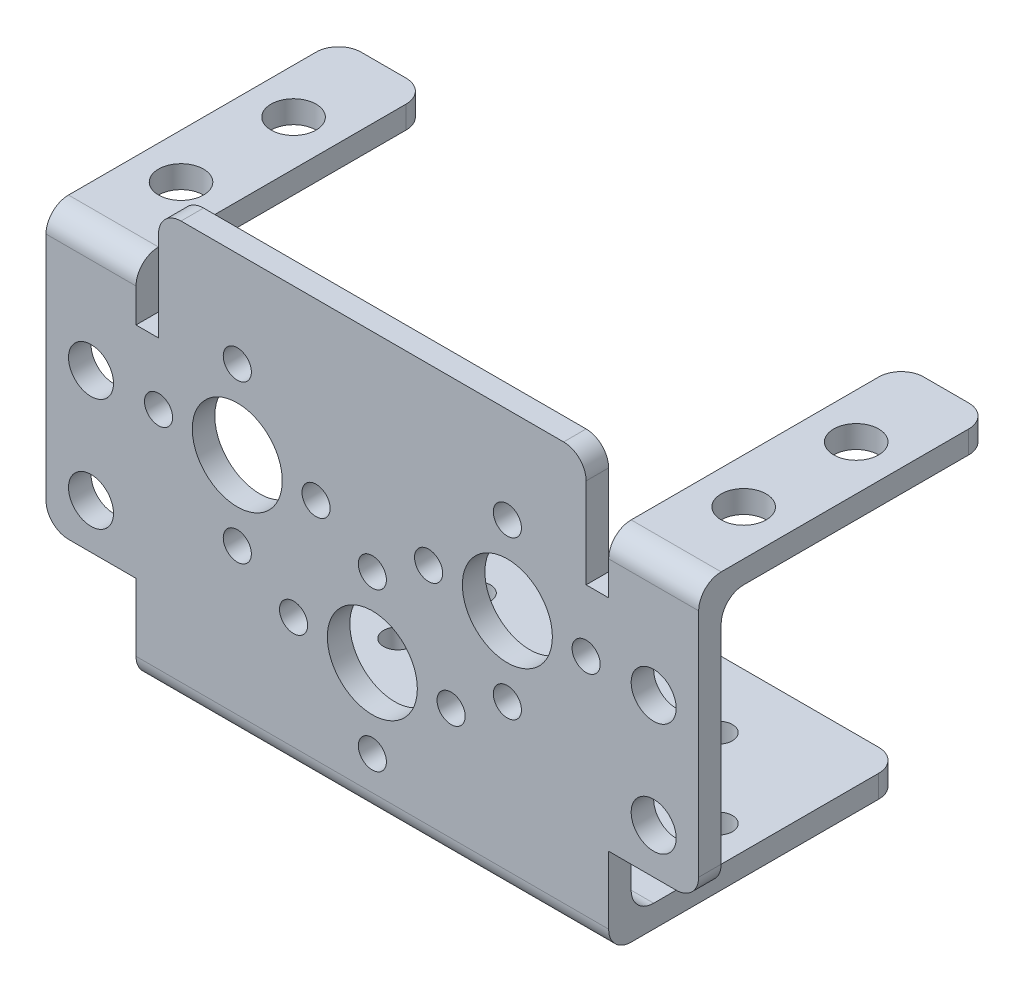
SolidWorks part; units mm, degrees
ref_plane "前视基准面" through (0, 0, 0) normal (0, 0, 1) x (1, 0, 0)
ref_plane "上视基准面" through (0, 0, 0) normal (0, 1, 0) x (1, 0, 0)
ref_plane "右视基准面" through (0, 0, 0) normal (1, 0, 0) x (0, 0, -1)
sketch "草图1" plane through (0, 0, 0) normal (0, 1, 0) x (1, 0, 0)
  line L0 (0, 0) -> (12, 0) construction
  line L1 (-21, 13) -> (21, 13)
  line L2 (-21, 13) -> (-21, -13)
  line L3 (-21, -13) -> (21, -13)
  line L4 (21, 13) -> (21, -13)
  line L5 (-21, 13) -> (21, -13) construction
  line L6 (-21, -13) -> (21, 13) construction
  line L7 (0, 0) -> (0, -13) construction
  circle A0 centre (10.75, 0) radius 1.25
  circle A1 centre (10.75, 0) radius 7 construction
  circle A2 centre (3.75, 0) radius 1.25
  circle A3 centre (10.75, 7) radius 1.25
  circle A4 centre (17.75, 0) radius 1.25
  circle A5 centre (10.75, -7) radius 1.25
  circle A6 centre (-10.75, -7) radius 1.25
  circle A7 centre (-17.75, 0) radius 1.25
  circle A8 centre (-10.75, 0) radius 1.25
  circle A9 centre (-10.75, 7) radius 1.25
  circle A10 centre (-3.75, 0) radius 1.25
  point P0 (0, 0)
  point P22 (10.75, 0)
  dimension "D4" = 2.5
  dimension "D5" = 14
  dimension "D6" = 2.5
  dimension "D8" = 7
  dimension "D1" = 42
  dimension "D2" = 26
  dimension "D3" = 12
  dimension "D9" = 7
  dimension "D7" = 4
extrude "凸台-拉伸1" add sketch "草图1" along normal blind 2
sketch "草图2" plane through (0, 0, 13) normal (0, 0, 1) x (1, 0, 0)
  line L3 (21, 0) -> (-21, 0)
  line L4 (0, 0) -> (0, 12) construction
  line L5 (0, 12) -> (0, 22) construction
  line L6 (0, 22) -> (12, 22) construction
  line L7 (0, 0) -> (0, 37.5) construction
  line L8 (0, 37.5) -> (-19, 37.5)
  line L9 (0, 37.5) -> (19, 37.5)
  line L10 (-19, 37.5) -> (-19, 27.5)
  line L11 (19, 37.5) -> (19, 27.5)
  line L12 (-19, 27.5) -> (-21, 27.5)
  line L13 (19, 27.5) -> (21, 27.5)
  line L16 (-21, 27.5) -> (-21, 32.5)
  line L17 (-21, 32.5) -> (-29, 32.5)
  line L18 (-29, 32.5) -> (-29, 8)
  line L19 (-29, 8) -> (-21, 8)
  line L20 (-21, 8) -> (-21, 0)
  line L21 (21, 8) -> (21, 0)
  line L22 (29, 8) -> (21, 8)
  line L23 (29, 32.5) -> (29, 8)
  line L24 (21, 32.5) -> (29, 32.5)
  line L25 (21, 27.5) -> (21, 32.5)
  line L26 (-19, 22) -> (-25, 22) construction
  line L27 (-25, 22) -> (-25, 12) construction
  circle A0 centre (0, 12) radius 4
  circle A1 centre (0, 12) radius 7 construction
  circle A2 centre (0, 19) radius 1.25
  circle A3 centre (7, 12) radius 1.25
  circle A4 centre (0, 5) radius 1.25
  circle A5 centre (-7, 12) radius 1.25
  circle A6 centre (12, 22) radius 4
  circle A7 centre (12, 22) radius 7 construction
  circle A8 centre (12, 29) radius 1.25
  circle A9 centre (19, 22) radius 1.25
  circle A10 centre (12, 15) radius 1.25
  circle A11 centre (5, 22) radius 1.25
  circle A12 centre (-19, 22) radius 1.25
  circle A13 centre (-12, 15) radius 1.25
  circle A14 centre (-12, 22) radius 4
  circle A15 centre (-5, 22) radius 1.25
  circle A16 centre (-12, 29) radius 1.25
  circle A17 centre (-25, 22) radius 2
  circle A18 centre (-25, 12) radius 2
  circle A19 centre (25, 12) radius 2
  circle A20 centre (25, 22) radius 2
  point P22 (0, 12)
  point P35 (12, 22)
  dimension "D3" = 8
  dimension "D4" = 14
  dimension "D5" = 2.5
  dimension "D11" = 8
  dimension "D12" = 14
  dimension "D13" = 2.5
  dimension "D27" = 4
  dimension "D29" = 4
  dimension "D2" = 12
  dimension "D7" = 7
  dimension "D8" = 7
  dimension "D9" = 10
  dimension "D10" = 12
  dimension "D15" = 7
  dimension "D16" = 7
  dimension "D17" = 19
  dimension "D18" = 19
  dimension "D19" = 10
  dimension "D20" = 10
  dimension "D21" = 37.5
  dimension "D22" = 2
  dimension "D23" = 5
  dimension "D24" = 8
  dimension "D25" = 24.5
  dimension "D26" = 6
  dimension "D28" = 10
  dimension "D6" = 4
  dimension "D14" = 4
extrude "凸台-拉伸2" add sketch "草图2" against normal blind 2
sketch "草图3" plane through (0, 32.5, 0) normal (0, 1, 0) x (1, 0, 0)
  line L0 (-29, -13) -> (-29, 13)
  line L1 (-29, 13) -> (-21, 13)
  line L2 (-21, 13) -> (-21, -13)
  line L3 (-21, -13) -> (-29, -13)
  line L4 (-25, 13) -> (-25, 5) construction
  line L5 (-25, 5) -> (-25, -5) construction
  line L6 (0, -13) -> (0, 13) construction
  line L7 (19, -13) -> (-19, -13) construction
  line L8 (21, 13) -> (-21, 13) construction
  line L9 (29, -13) -> (29, 13)
  line L10 (29, 13) -> (21, 13)
  line L11 (21, 13) -> (21, -13)
  line L12 (21, -13) -> (29, -13)
  circle A0 centre (-25, 5) radius 2
  circle A1 centre (-25, -5) radius 2
  circle A2 centre (25, -5) radius 2
  circle A3 centre (25, 5) radius 2
  dimension "D3" = 4
  dimension "D5" = 4
  dimension "D1" = 26
  dimension "D2" = 8
  dimension "D4" = 10
extrude "凸台-拉伸3" add sketch "草图3" against normal blind 2
fillet "圆角1" radius 2 16 edges at (19, 37.5, 12) (-19, 37.5, 12) (-21, 31.5, -13) (-29, 31.5, -13) (29, 31.5, -13) (21, 31.5, -13) (21, 1, -13) (-21, 1, -13) (25, 30.5, 11) (-25, 30.5, 11) (0, 2, 11) (-25, 32.5, 13) (0, 0, 13) (25, 32.5, 13) (29, 8, 12) (-29, 8, 12)
